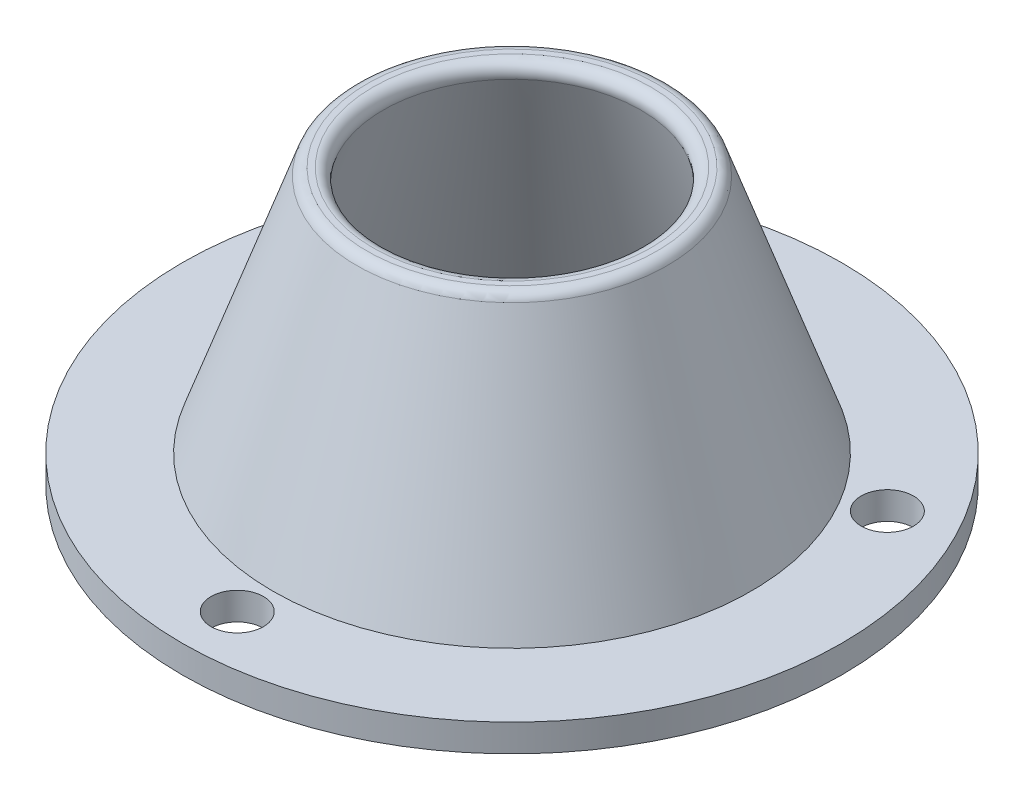
SolidWorks part; units mm, degrees
ref_plane "Alzado" through (0, 0, 0) normal (0, 0, 1) x (1, 0, 0)
ref_plane "Planta" through (0, 0, 0) normal (0, 1, 0) x (1, 0, 0)
ref_plane "Vista lateral" through (0, 0, 0) normal (1, 0, 0) x (0, 0, -1)
sketch "Croquis2" plane through (0, 0, 0) normal (0, 0, 1) x (1, 0, 0)
  line L0 (0, 0) -> (0, 382.4464) construction
  line L1 (0, 0) -> (378.1156, 0) construction
  line L2 (40, 0) -> (60, 0)
  line L3 (60, 0) -> (60, 5)
  line L4 (43.5474, 5) -> (28.2662, 48.6607)
  line L5 (26.3784, 50) -> (25.319, 50)
  line L8 (43.5474, 5) -> (60, 5)
  line L9 (40, 0) -> (23.4312, 47.3393)
  arc A0 (26.3784, 50) -> (28.2662, 48.6607) centre (26.3784, 48) cw
  arc A1 (23.4312, 47.3393) -> (25.319, 50) centre (25.319, 48) cw
  point P15 (22.5, 50)
  dimension "D7" = 2
  dimension "D8" = 2
  dimension "D1" = 22.5
  dimension "D2" = 5
  dimension "D3" = 5
  dimension "D4" = 40
  dimension "D5" = 50
  dimension "D6" = 60
revolve "Revolución1" add sketch "Croquis2" angle 360 about L0
sketch "Croquis3" plane through (0, 0, 0) normal (0, -1, 0) x (1, 0, 0)
  line L0 (0, 67.16) -> (0, -73.5317) construction
  line L1 (-70.8442, 40.9019) -> (99.5082, -57.4511) construction
  line L2 (76.7423, 44.3072) -> (-66.8004, -38.5672) construction
  circle A0 centre (0, 50) radius 4.7625
  circle A1 centre (0, 0) radius 60 construction
  circle A2 centre (43.3013, -25) radius 4.7625
  circle A3 centre (-43.3013, -25) radius 4.7625
  circle A4 centre (0, 0) radius 50
  dimension "D3" = 9.525
  dimension "D4" = 10
  dimension "D1" = 60
  dimension "D2" = 60
  dimension "D5" = 3
extrude "Cortar-Extruir2" cut sketch "Croquis3" against normal blind 10 contours A4 A0 | A0 A4 | A3 A4 | A4 A3 | A4 A2 | A2 A4
